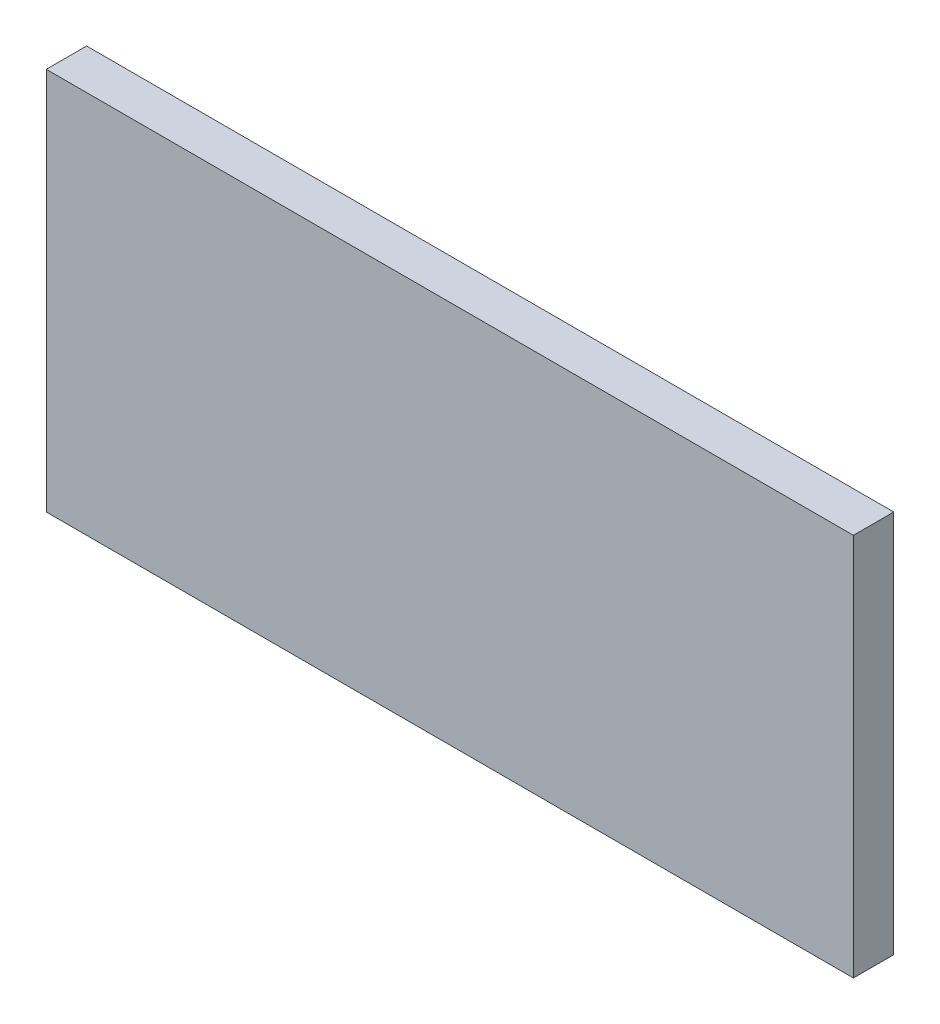
SolidWorks part; units mm, degrees
ref_plane "Front" through (0, 0, 0) normal (0, 0, 1) x (1, 0, 0)
ref_plane "Top" through (0, 0, 0) normal (0, 1, 0) x (1, 0, 0)
ref_plane "Right" through (0, 0, 0) normal (1, 0, 0) x (0, 0, -1)
sketch "草图1" plane through (0, 0, 0) normal (0, 0, 1) x (1, 0, 0)
  line L1 (0, 0) -> (40, 0)
  line L2 (0, 0) -> (0, 19)
  line L3 (0, 19) -> (40, 19)
  line L4 (40, 0) -> (40, 19)
extrude "凸台-拉伸1" add sketch "草图1" along normal blind 2
